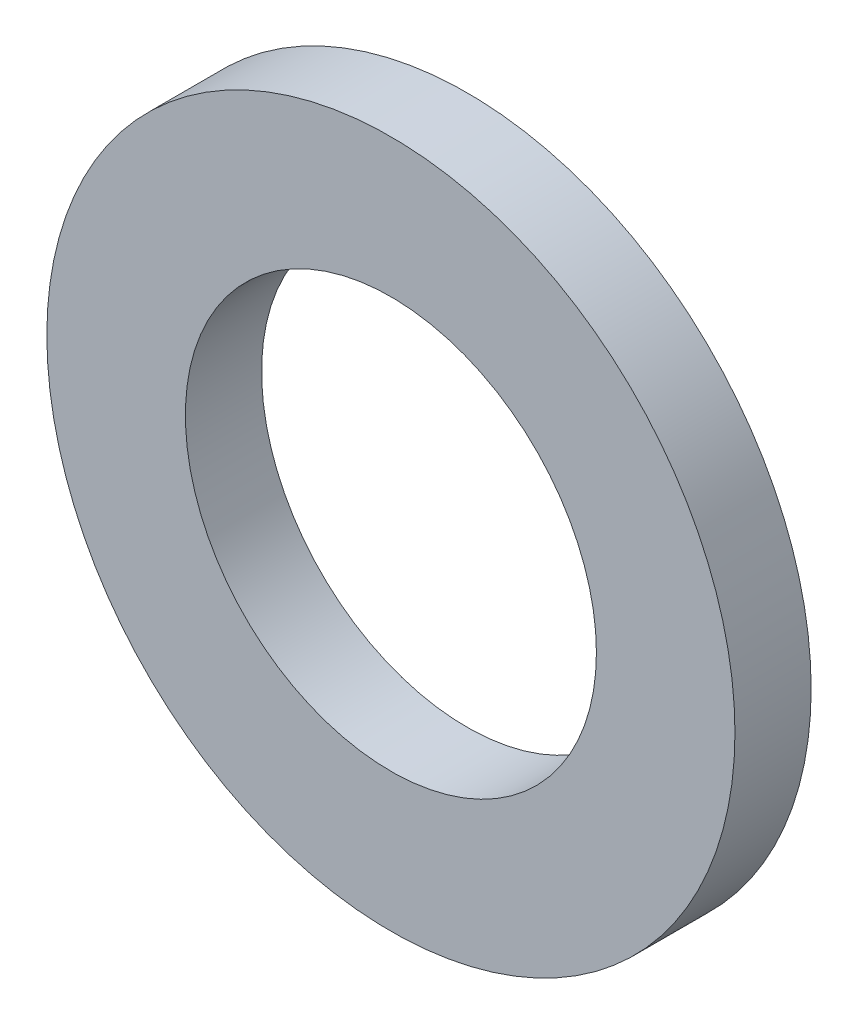
SolidWorks part; units mm, degrees
ref_plane "Front Plane" through (0, 0, 0) normal (0, 0, 1) x (1, 0, 0)
ref_plane "Top Plane" through (0, 0, 0) normal (0, 1, 0) x (1, 0, 0)
ref_plane "Right Plane" through (0, 0, 0) normal (1, 0, 0) x (0, 0, -1)
sketch "Sketch1" plane through (0, 0, 0) normal (0, 0, 1) x (1, 0, 0)
  line L0 (-1.8923, 0) -> (1.8923, 0) construction
  line L1 (0, -1.8923) -> (0, 1.8923) construction
  circle A0 centre (0, 0) radius 1.8923
  circle A1 centre (0, 0) radius 1.1303
  point P4 (0, 0)
  point P9 (0, 0)
  dimension "ID" = 2.2606
  dimension "OD" = 3.7846
sketch "Sketch2" plane through (0, 0, 0) normal (1, 0, 0) x (0, 0, -1)
  line L0 (0.2095, 1.8923) -> (-0.2095, 1.8923) construction
  line L1 (0, 1.8923) -> (0, -1.8923) construction
  point P4 (0, 1.8923)
  dimension "Thickness" = 0.4191
sketch "Sketch3" plane through (0, 0, 0) normal (0, 0, 1) x (1, 0, 0)
  line L0 (0, -1.8923) -> (0, 1.8923) construction
  circle A0 centre (0, 0) radius 1.8923
  circle A1 centre (0, 0) radius 1.1303
  circle A2 centre (0, 0) radius 1.1303 construction
extrude "Boss-Extrude1" add sketch "Sketch3" along normal mid plane 0.4191
equation "\"D1@Boss-Extrude1\" = \"Thickness@Sketch2\""
